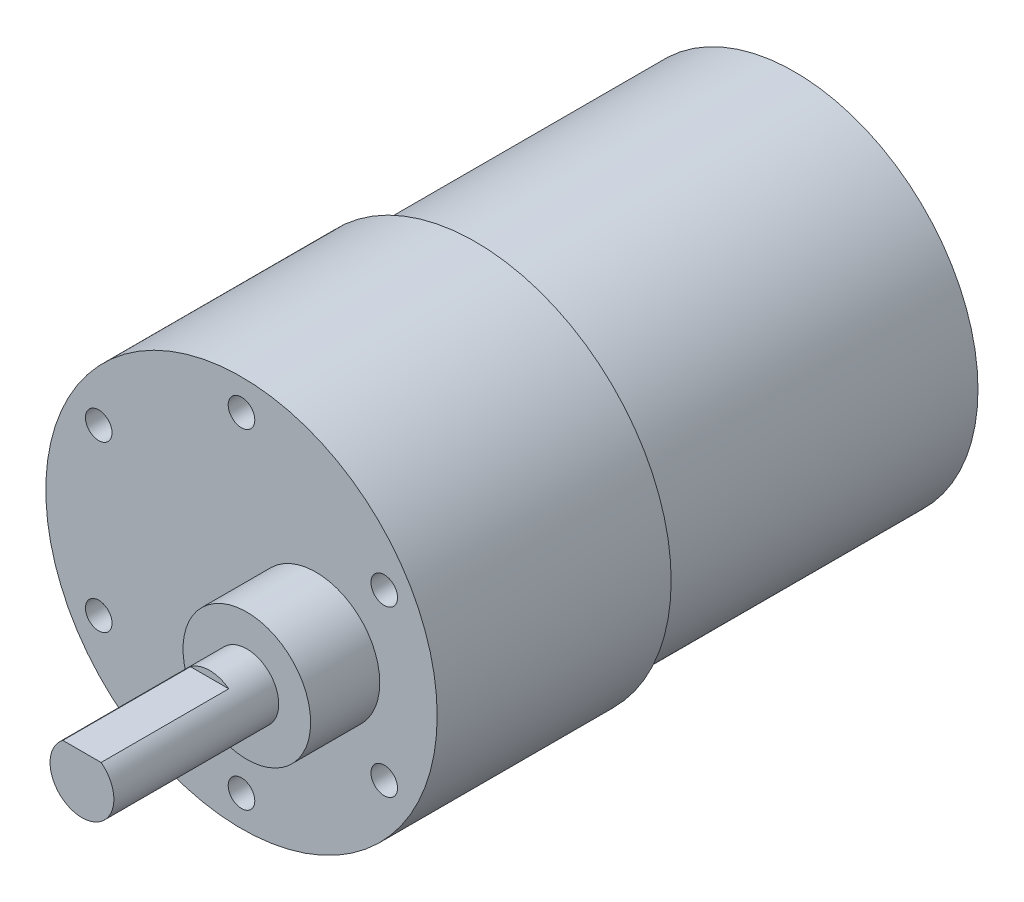
SolidWorks part; units mm, degrees
ref_plane "Front Plane" through (0, 0, 0) normal (0, 0, 1) x (1, 0, 0)
ref_plane "Top Plane" through (0, 0, 0) normal (0, 1, 0) x (1, 0, 0)
ref_plane "Right Plane" through (0, 0, 0) normal (1, 0, 0) x (0, 0, -1)
sketch "Sketch1" plane through (0, 0, 0) normal (0, 0, 1) x (1, 0, 0)
  circle A0 centre (0, 0) radius 18.4
  dimension "D1" = 36.8
extrude "Boss-Extrude1" add sketch "Sketch1" along normal blind 22
sketch "Sketch2" plane through (0, 0, 22) normal (0, 0, 1) x (1, 0, 0)
  line L1 (0, 15.5) -> (-13.4234, 7.75)
  line L2 (-13.4234, 7.75) -> (-13.4234, -7.75)
  line L3 (-13.4234, -7.75) -> (0, -15.5)
  line L4 (0, -15.5) -> (13.4234, -7.75)
  line L5 (13.4234, -7.75) -> (13.4234, 7.75)
  line L6 (13.4234, 7.75) -> (0, 15.5)
  circle A0 centre (0, 0) radius 13.4234 construction
  dimension "D1" = 15.5
hole_wizard "M3x0.5 Tapped Hole1" positions "Sketch4" profile "Sketch3" tap size "M3x0.5" standard "Ansi Metric"
sketch "Sketch4" plane through (0, 0, 22) normal (0, 0, 1) x (1, 0, 0)
  point P0 (-13.4234, 7.75)
  point P1 (0, 15.5)
  point P4 (13.4234, 7.75)
  point P7 (13.4234, -7.75)
  point P10 (0, -15.5)
  point P13 (-13.4234, -7.75)
sketch "Sketch3" plane through (-13.4234, 7.75, 22) normal (1, 0, 0) x (0, -1, 0)
  line L0 (0, 0) -> (0, 8.3711)
  line L1 (0, 8.3711) -> (1.25, 7.62)
  line L2 (1.25, 7.62) -> (1.25, 0)
  line L5 (1.25, 0) -> (0, 0)
  line L10 (0, 8.3711) -> (-1.25, 7.62) construction
  line L11 (0, -6.35) -> (0, 107.95) construction
  dimension "Tap Drill Dia." = 2.5
  dimension "Tap Drill Depth" = 7.62
  dimension "Drill Angle" = 118
cosmetic thread "Hole Thread1" parameters "D1"=6.096, "D2"=3
cosmetic thread "Hole Thread2" parameters "D1"=6.096, "D2"=3
cosmetic thread "Hole Thread3" parameters "D1"=6.096, "D2"=3
cosmetic thread "Hole Thread4" parameters "D1"=6.096, "D2"=3
cosmetic thread "Hole Thread5" parameters "D1"=6.096, "D2"=3
cosmetic thread "Hole Thread6" parameters "D1"=6.096, "D2"=3
sketch "Sketch6" plane through (0, 0, 0) normal (0, 0, -1) x (-1, 0, 0)
  circle A0 centre (0, 0) radius 17.25
  dimension "D1" = 34.5
extrude "Boss-Extrude2" add sketch "Sketch6" along normal blind 30
sketch "Sketch7" plane through (0, 0, 22) normal (0, 0, 1) x (1, 0, 0)
  circle A0 centre (7, 0) radius 3
  dimension "D1" = 6
  dimension "D2" = 7
extrude "Boss-Extrude3" add sketch "Sketch7" along normal blind 22
sketch "Sketch8" plane through (0, 0, 44) normal (0, 0, 1) x (1, 0, 0)
  line L0 (5.2, 2.4) -> (8.8, 2.4)
  circle A0 centre (7, 0) radius 3 construction
  arc A1 (8.8, 2.4) -> (5.2, 2.4) centre (7, 0) ccw
  dimension "D1" = 5.4
extrude "Cut-Extrude1" cut sketch "Sketch8" against normal blind 12
sketch "Sketch9" plane through (0, 0, 22) normal (0, 0, 1) x (1, 0, 0)
  circle A0 centre (7, 0) radius 6
  dimension "D1" = 12
extrude "Boss-Extrude4" add sketch "Sketch9" along normal blind 6.5
sketch "Sketch10" plane through (0, 0, 22) normal (0, 0, 1) x (1, 0, 0)
  line L0 (7, 0) -> (0, 0)
